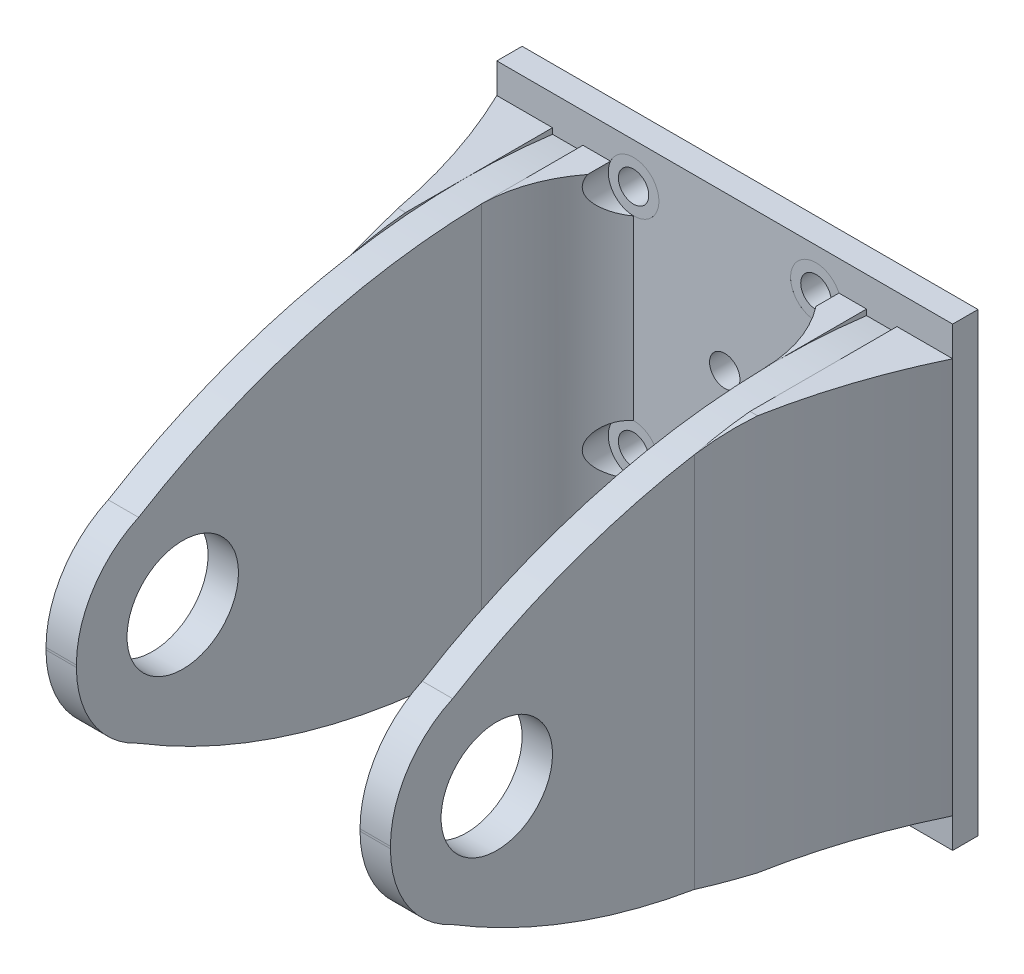
SolidWorks part; units mm, degrees
ref_plane "前视基准面" through (0, 0, 0) normal (0, 0, 1) x (1, 0, 0)
ref_plane "上视基准面" through (0, 0, 0) normal (0, 1, 0) x (1, 0, 0)
ref_plane "右视基准面" through (0, 0, 0) normal (1, 0, 0) x (0, 0, -1)
sketch "草图1" plane through (0, 0, 0) normal (0, 0, 1) x (1, 0, 0)
  line L1 (0, 0) -> (45, 0)
  line L2 (0, 0) -> (0, 45)
  line L3 (0, 45) -> (45, 45)
  line L4 (45, 0) -> (45, 45)
  dimension "D1" = 45
extrude "凸台-拉伸1" add sketch "草图1" along normal blind 2.5
ref_plane "基准面1" through (0, 0, 2.5) normal (0, 0, 1) x (1, 0, 0)
sketch "草图2" plane through (0, 0, 2.5) normal (0, 0, 1) x (1, 0, 0)
  line L0 (22.5, 45) -> (22.5, 12.6233) construction
  line L1 (45, 45) -> (0, 45) construction
  line L2 (0, 22.5) -> (22.5, 22.5) construction
  line L3 (0, 45) -> (0, 0) construction
  line L4 (22.5, 22.5) -> (36.5, 22.5) construction
  line L5 (36.5, 22.5) -> (36.5, 0)
  line L6 (0, 0) -> (45, 0) construction
  line L7 (36.5, 0) -> (39.5, 0)
  line L8 (39.5, 0) -> (39.5, 45)
  line L9 (39.5, 45) -> (36.5, 45)
  line L10 (36.5, 45) -> (36.5, 22.5)
  line L11 (8.5, 45) -> (8.5, 22.5)
  line L12 (5.5, 45) -> (8.5, 45)
  line L13 (5.5, 0) -> (5.5, 45)
  line L14 (8.5, 0) -> (5.5, 0)
  line L15 (8.5, 22.5) -> (8.5, 0)
  dimension "D1" = 14
  dimension "D2" = 3
extrude "凸台-拉伸2" add sketch "草图2" along normal blind 50
ref_plane "基准面2" through (39.5, 0, 0) normal (1, 0, 0) x (0, 0, -1)
sketch "草图3" plane through (39.5, 0, 0) normal (1, 0, 0) x (0, 0, -1)
  line L0 (-52.5, 22.5) -> (-42, 22.5) construction
  line L1 (-52.5, 0) -> (-52.5, 45) construction
  line L2 (-27.5, 45) -> (-27.5, 22.5) construction
  line L3 (-52.5, 45) -> (-2.5, 45) construction
  circle A0 centre (-42, 22.5) radius 5.5
  circle A1 centre (-42, 22.5) radius 10.5 construction
  dimension "D2" = 11
  dimension "D3" = 21
  dimension "D1" = 10.5
extrude "切除-拉伸1" cut sketch "草图3" against normal through all
sketch "草图4" plane through (39.5, 0, 0) normal (1, 0, 0) x (0, 0, -1)
  line L0 (-2.5, 45) -> (-2.5, 41.4742)
  line L1 (-42, 22.605) -> (-52.5, 22.605) construction
  line L2 (-2.5, 27.2281) -> (-2.5, -27.2281) construction
  line L3 (-52.5, 22.605) -> (-52.5, 45)
  line L4 (-52.5, 45) -> (-2.5, 45)
  line L5 (-2.5, 22.5) -> (-57.8273, 22.5) construction
  line L7 (-52.5, 0) -> (-52.5, 45) construction
  line L8 (-52.5, 22.395) -> (-52.5, 0)
  line L9 (-52.5, 0) -> (-2.5, 0)
  line L10 (-2.5, 0) -> (-2.5, 3.5258)
  arc A0 (-46.3587, 32.1576) -> (-52.5, 22.605) centre (-42, 22.605) ccw
  arc A1 (-46.3587, 32.1576) -> (-2.5, 41.4742) centre (-11.2034, -25.4458) cw
  arc A2 (-46.3587, 12.8424) -> (-52.5, 22.395) centre (-42, 22.395) cw
  arc A3 (-46.3587, 12.8424) -> (-2.5, 3.5258) centre (-11.2034, 70.4458) ccw
  dimension "D1" = 10.5
extrude "切除-拉伸2" cut sketch "草图4" against normal through all
ref_plane "基准面3" through (0, 0, 2.5) normal (0, 0, 1) x (1, 0, 0)
sketch "草图5" plane through (0, 0, 2.5) normal (0, 0, 1) x (1, 0, 0)
  line L0 (7, 2.9622) -> (13.5, 2.9622) construction
  line L1 (5.5, 2.9622) -> (8.5, 2.9622) construction
  line L2 (22.5, 45) -> (22.5, 26.1335) construction
  line L3 (8.5, 42.0378) -> (13.5, 42.0378)
  line L4 (8.5, 42.0378) -> (8.5, 2.9622)
  line L5 (8.5, 2.9622) -> (13.5, 2.9622)
  line L6 (13.5, 42.0378) -> (13.5, 2.9622)
  line L7 (45, 45) -> (0, 45) construction
  line L8 (36.5, 2.9622) -> (31.5, 2.9622)
  line L9 (31.5, 42.0378) -> (31.5, 2.9622)
  line L10 (36.5, 42.0378) -> (31.5, 42.0378)
  line L11 (36.5, 42.0378) -> (36.5, 2.9622)
  dimension "D1" = 5
extrude "凸台-拉伸3" add sketch "草图5" along normal blind 10
ref_plane "基准面4" through (0, 42.0378, 0) normal (0, 1, 0) x (1, 0, 0)
sketch "草图6" plane through (0, 42.0378, 0) normal (0, 1, 0) x (1, 0, 0)
  line L0 (-27.2281, -2.5) -> (27.2281, -2.5) construction
  line L1 (22.5, 0) -> (22.5, -12.7067) construction
  line L2 (13.5, -2.5) -> (13.5, -12.5)
  line L3 (13.5, -12.5) -> (8.5, -12.5)
  line L4 (45, 0) -> (0, 0) construction
  line L5 (31.5, -2.5) -> (31.5, -12.5)
  line L6 (31.5, -12.5) -> (36.5, -12.5)
  arc A0 (8.5, -12.5) -> (13.5, -2.5) centre (21.4135, -12.7067) cw
  arc A1 (36.5, -12.5) -> (31.5, -2.5) centre (23.5865, -12.7067) ccw
extrude "切除-拉伸3" cut sketch "草图6" against normal through all
sketch "草图7" plane through (0, 0, 2.5) normal (0, 0, 1) x (1, 0, 0)
  line L0 (5.5, 2.9622) -> (0, 2.9622)
  line L1 (0, 45) -> (0, 0) construction
  line L2 (0, 2.9622) -> (0, 42.0378)
  line L3 (7.5018, 42.0378) -> (-7.5018, 42.0378) construction
  line L4 (0, 42.0378) -> (5.5, 42.0378)
  line L5 (5.5, 42.0378) -> (5.5, 32.1576) construction
  line L6 (5.5, 42.0378) -> (5.5, 2.9622)
  line L7 (45, 45) -> (0, 45) construction
  line L8 (22.5, 45) -> (22.5, 17.548) construction
  line L9 (45, 42.0378) -> (39.5, 42.0378)
  line L10 (45, 2.9622) -> (45, 42.0378)
  line L11 (39.5, 2.9622) -> (45, 2.9622)
  line L12 (39.5, 42.0378) -> (39.5, 2.9622)
extrude "凸台-拉伸4" add sketch "草图7" along normal blind 20
ref_plane "基准面5" through (45, 0, 0) normal (1, 0, 0) x (0, 0, -1)
sketch "草图8" plane through (45, 0, 0) normal (1, 0, 0) x (0, 0, -1)
  line L0 (7.5018, 42.0378) -> (-7.5018, 42.0378) construction
  line L1 (-22.5, 41.0856) -> (-22.5, 42.0378)
  line L2 (-22.5, 42.0378) -> (-17.0082, 42.0378)
  line L3 (-22.5, 22.5) -> (-17.0082, 22.5) construction
  line L4 (-22.5, 41.0856) -> (-22.5, 3.9144) construction
  line L5 (-22.5, 3.9144) -> (-22.5, 2.9622)
  line L6 (-22.5, 2.9622) -> (-17.0082, 2.9622)
  arc A0 (-22.5, 41.0856) -> (-17.0082, 42.0378) centre (-13.2942, 4.3055) cw
  arc A1 (-22.5, 3.9144) -> (-17.0082, 2.9622) centre (-13.2942, 40.6945) ccw
extrude "切除-拉伸4" cut sketch "草图8" against normal through all
ref_plane "基准面6" through (0, 2.9622, 0) normal (0, -1, 0) x (-1, 0, 0)
sketch "草图9" plane through (0, 2.9622, 0) normal (0, -1, 0) x (-1, 0, 0)
  line L0 (-39.5, 31.1415) -> (-39.5, -31.1415) construction
  line L1 (-45, -22.5) -> (-39.5, -22.5) construction
  line L2 (-45, 1.375) -> (-45, -1.375) construction
  line L3 (-32.441, -2.5) -> (32.441, -2.5) construction
  line L6 (0, 0) -> (-45, 0) construction
  line L7 (-22.5, 0) -> (-22.5, -19.4482) construction
  line L8 (-39.5, -22.5) -> (-45, -22.5)
  line L9 (-45, -22.5) -> (-45, -2.5)
  line L10 (-5.5, -22.5) -> (0, -22.5)
  line L11 (0, -22.5) -> (0, -2.5)
  arc A0 (-39.5, -22.5) -> (-45, -2.5) centre (-96.727, -27.4812) ccw
  arc A1 (-5.5, -22.5) -> (0, -2.5) centre (51.727, -27.4812) cw
extrude "切除-拉伸5" cut sketch "草图9" against normal through all
sketch "草图12" plane through (0, 0, 0) normal (0, 0, -1) x (-1, 0, 0)
  line L0 (-22.5, 41) -> (-22.5, 18.5) construction
  line L1 (-45, 45) -> (0, 45) construction
  line L2 (-13.5, 18.5) -> (-31.5, 18.5) construction
  line L3 (-13.5, 18.5) -> (-13.5, 41) construction
  line L4 (-13.5, 41) -> (-31.5, 41) construction
  line L5 (-31.5, 18.5) -> (-31.5, 41) construction
  circle A0 centre (-13.5, 18.5) radius 1.5
  circle A1 centre (-13.5, 6.5) radius 1.5253
  circle A2 centre (-31.5, 18.5) radius 1.5
  circle A3 centre (-31.5, 6.5) radius 1.4505
  circle A4 centre (-13.5, 41) radius 1.5
  circle A5 centre (-31.5, 41) radius 1.5
  circle A6 centre (-22.5, 29.75) radius 1.5
  dimension "D2" = 3
  dimension "D3" = 3
  dimension "D1" = 4
extrude "切除-拉伸7" cut sketch "草图12" against normal up to next
sketch "草图13" plane through (0, 0, 2.5) normal (0, 0, 1) x (1, 0, 0)
  line L0 (22.5, 29.75) -> (22.5, 25.1074) construction
  line L5 (22.5, 29.75) -> (17.246, 29.75) construction
  circle A0 centre (13.5, 6.5) radius 2.5
  circle A1 centre (13.5, 18.5) radius 2.5
  circle A2 centre (13.5, 41) radius 2.5
  circle A3 centre (31.5, 41) radius 2.5
  circle A4 centre (31.5, 18.5) radius 2.5
  circle A5 centre (31.5, 6.5) radius 2.5
  dimension "D3" = 5
  dimension "D1" = 12
extrude "切除-拉伸8" cut sketch "草图13" against normal offset from surface 0.001 and the other way blind 10 up to face at (21, 29.75, 2.5)
